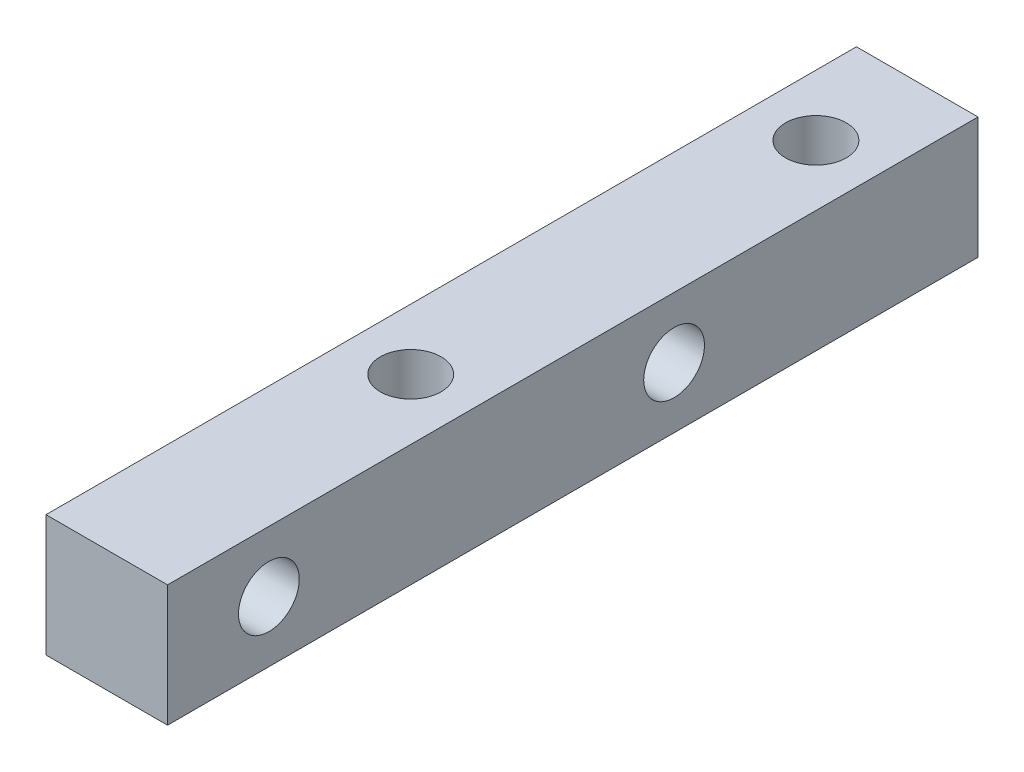
SolidWorks part; units mm, degrees
material "6061-T6 (SS)"
ref_plane "前视基准面" through (0, 0, 0) normal (0, 0, 1) x (1, 0, 0)
ref_plane "上视基准面" through (0, 0, 0) normal (0, 1, 0) x (1, 0, 0)
ref_plane "右视基准面" through (0, 0, 0) normal (1, 0, 0) x (0, 0, -1)
sketch "草图1" plane through (0, 0, 0) normal (0, 0, 1) x (1, 0, 0)
  line L1 (0, 0) -> (6, 0)
  line L2 (0, 0) -> (0, 6)
  line L3 (0, 6) -> (6, 6)
  line L4 (6, 0) -> (6, 6)
  dimension "D1" = 6
  dimension "D2" = 6
extrude "凸台-拉伸1" add sketch "草图1" along normal blind 40
sketch "草图2" plane through (0, 6, 0) normal (0, 1, 0) x (1, 0, 0)
  line L0 (3, 0) -> (3, -5) construction
  line L1 (6, 0) -> (0, 0) construction
  line L2 (3, -5) -> (3, -25) construction
  circle A0 centre (3, -5) radius 1.5
  circle A1 centre (3, -25) radius 1.5
  dimension "D1" = 3
  dimension "D2" = 5
  dimension "D3" = 20
extrude "切除-拉伸1" cut sketch "草图2" against normal blind 50
cosmetic thread "装饰螺纹线1" [suppressed] parameters "D2"=4
cosmetic thread "装饰螺纹线3" [suppressed] parameters "D2"=4
sketch "草图3" plane through (0, 0, 0) normal (-1, 0, 0) x (0, 0, 1)
  line L0 (0, 3) -> (15, 3) construction
  line L1 (0, 6) -> (0, 0) construction
  line L2 (15, 3) -> (35, 3) construction
  circle A0 centre (35, 3) radius 1.5
  circle A1 centre (15, 3) radius 1.5
  dimension "D3" = 3
  dimension "D1" = 15
  dimension "D2" = 20
extrude "切除-拉伸2" cut sketch "草图3" against normal blind 50
cosmetic thread "装饰螺纹线2" [suppressed] parameters "D2"=4
cosmetic thread "装饰螺纹线4" [suppressed] parameters "D2"=4
